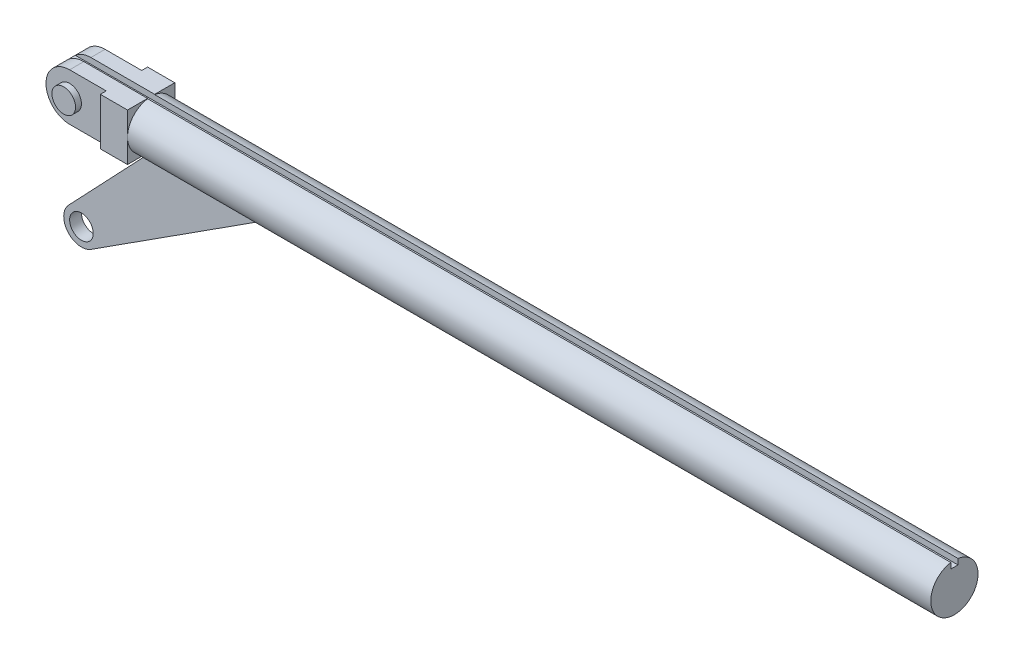
SolidWorks part; units mm, degrees
material "普通碳钢"
ref_plane "前视基准面" through (0, 0, 0) normal (0, 0, 1) x (1, 0, 0)
ref_plane "上视基准面" through (0, 0, 0) normal (0, 1, 0) x (1, 0, 0)
ref_plane "右视基准面" through (0, 0, 0) normal (1, 0, 0) x (0, 0, -1)
sketch "草图1" plane through (0, 0, 0) normal (1, 0, 0) x (0, 0, -1)
  circle A0 centre (0, 0) radius 2
  dimension "D1" = 4
extrude "凸台-拉伸1" add sketch "草图1" against normal blind 68
sketch "草图2" plane through (0, 0, 0) normal (0, 0, 1) x (1, 0, 0)
  line L0 (-68, -2) -> (0, -2) construction
  line L1 (-68, 2) -> (-73.4, 2)
  line L2 (-68, 2) -> (-68, -2)
  line L3 (-68, -2) -> (-73.4, -2)
  arc A0 (-73.4, 2) -> (-73.4, -2) centre (-73.4, 0) ccw
  dimension "D1" = 5.4
extrude "凸台-拉伸2" add sketch "草图2" along normal mid plane 4
sketch "草图3" plane through (0, 0, 0) normal (0, 1, 0) x (1, 0, 0)
  line L0 (-68, 0) -> (-68, 2) construction
  line L1 (-75.4, 2) -> (-70.3, 2)
  line L2 (-75.4, 2) -> (-75.4, 1.5)
  line L3 (-75.4, 1.5) -> (-70.3, 1.5)
  line L4 (-70.3, 2) -> (-70.3, 1.5)
  line L5 (-75.4, -2) -> (-70.3, -2)
  line L6 (-75.4, -2) -> (-75.4, -1.5)
  line L7 (-75.4, -1.5) -> (-70.3, -1.5)
  line L8 (-70.3, -2) -> (-70.3, -1.5)
  dimension "D1" = 2.3
  dimension "D2" = 3
extrude "切除-拉伸1" cut sketch "草图3" against normal through all both and the other way through all
sketch "草图4" plane through (0, 0, 0) normal (0, 0, 1) x (1, 0, 0)
  circle A0 centre (-73.4, 0) radius 1
  dimension "D1" = 2
extrude "凸台-拉伸3" add sketch "草图4" along normal mid plane 4
sketch "草图5" plane through (0, 2, 0) normal (0, 1, 0) x (1, 0, 0)
  line L0 (-75.4, 1.5) -> (-75.4, -1.5) construction
  line L1 (-75.4, 0.3) -> (0, 0.3)
  line L2 (-75.4, 0.3) -> (-75.4, -0.3)
  line L3 (-75.4, -0.3) -> (0, -0.3)
  line L4 (0, 0.3) -> (0, -0.3)
  line L5 (0, -2) -> (0, 2) construction
  dimension "D1" = 0.6
extrude "切除-拉伸2" cut sketch "草图5" against normal blind 0.5
sketch "草图6" plane through (0, 0, 0) normal (0, 0, 1) x (1, 0, 0)
  line L0 (-67.4, -1.5) -> (-57.4, -1.5)
  line L1 (-57.4, -1.5) -> (-72.589, -11.2619)
  line L2 (-74.4879, -8.9673) -> (-67.4, -1.5)
  line L3 (-73.4, -10) -> (-73.4, 0) construction
  arc A0 (-72.589, -11.2619) -> (-74.4879, -8.9673) centre (-73.4, -10) cw
  circle A1 centre (-73.4, -10) radius 1
  circle A2 centre (-73.4, 0) radius 1 construction
  arc A3 (-73.4, 2) -> (-73.4, -2) centre (-73.4, 0) ccw construction
  dimension "D4" = 1.5
  dimension "D5" = 2
  dimension "D6" = 10
  dimension "D1" = 10
  dimension "D2" = 6
  dimension "D3" = 1.5
extrude "凸台-拉伸4" add sketch "草图6" along normal mid plane 1
